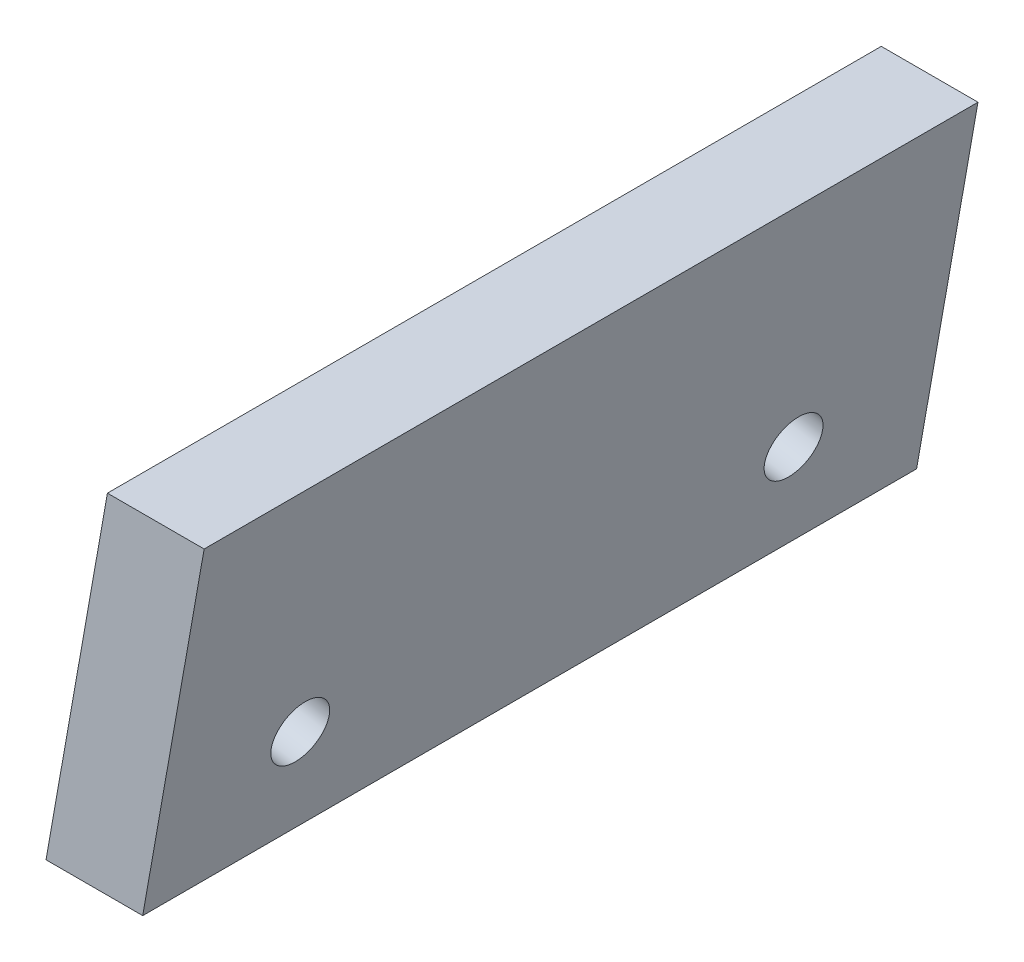
SolidWorks part; units mm, degrees
ref_plane "Front Plane" through (0, 0, 0) normal (0, 0, 1) x (1, 0, 0)
ref_plane "Top Plane" through (0, 0, 0) normal (0, 1, 0) x (1, 0, 0)
ref_plane "Right Plane" through (0, 0, 0) normal (1, 0, 0) x (0, 0, -1)
sketch "Sketch2" plane through (0, 0, 0) normal (0, 0, 1) x (1, 0, 0)
  line L0 (0, 0) -> (2.5, 0)
  line L1 (0, 0) -> (1.5869, 9)
  line L2 (2.5, 0) -> (4.0869, 9)
  line L3 (4.0869, 9) -> (1.5869, 9)
  line L4 (2.5, 0) -> (7.5011, 0) construction
  dimension "D1" = 9
  dimension "D2" = 2.5
  dimension "D3" = 80
extrude "Boss-Extrude2" add sketch "Sketch2" along normal blind 20
sketch "Sketch4" plane through (0, 0, 0) normal (-0.9848, 0.1736, 0) x (0, 0, 1)
  line L0 (0, 9.1388) -> (0, 0) construction
  line L1 (20, 9.1388) -> (20, 0) construction
  line L2 (20, 0) -> (0, 0) construction
  circle A0 centre (3.625, 3) radius 0.75
  circle A1 centre (16.375, 3) radius 0.75
  dimension "D1" = 3.625
  dimension "D2" = 3.625
  dimension "D3" = 3
  dimension "D4" = 3
  dimension "D5" = 1.5
  dimension "D6" = 1.5
extrude "Cut-Extrude1" cut sketch "Sketch4" against normal through all
